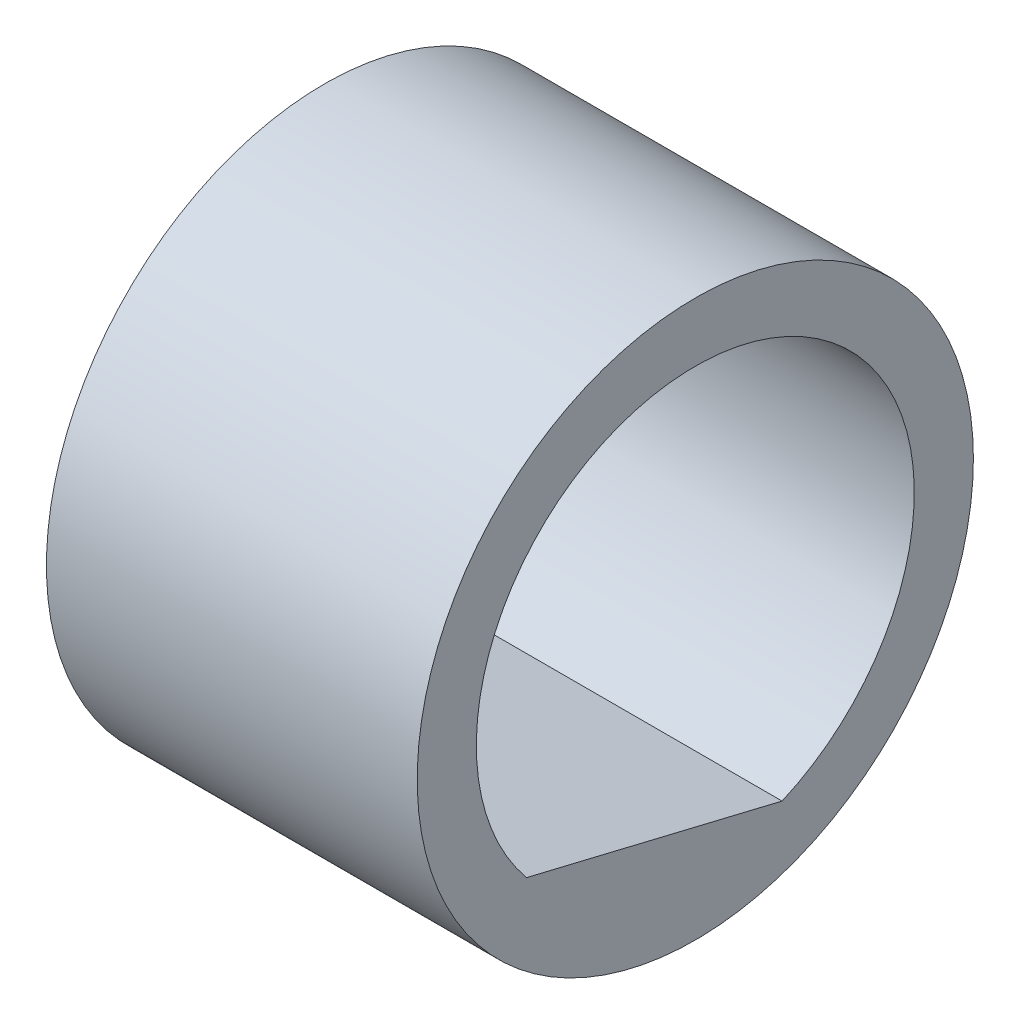
SolidWorks part; units mm, degrees
ref_plane "Front Plane" through (0, 0, 0) normal (0, 0, 1) x (1, 0, 0)
ref_plane "Top Plane" through (0, 0, 0) normal (0, 1, 0) x (1, 0, 0)
ref_plane "Right Plane" through (0, 0, 0) normal (1, 0, 0) x (0, 0, -1)
sketch "Sketch1" plane through (0, 0, 0) normal (1, 0, 0) x (0, 0, -1)
  circle A0 centre (0, 0) radius 3.81
  dimension "D1" = 7.62
extrude "Boss-Extrude1" add sketch "Sketch1" along normal blind 5.08
sketch "Sketch2" plane through (0, 0, 0) normal (-1, 0, 0) x (0, 0, 1)
  line L0 (2.3113, -1.9125) -> (-1.1889, -2.7544) construction
  line L1 (2.3113, -1.9125) -> (-1.1889, -2.7544)
  arc A0 (2.3113, -1.9125) -> (-1.1889, -2.7544) centre (0, 0) ccw construction
  arc A1 (2.3113, -1.9125) -> (-1.1889, -2.7544) centre (0, 0) ccw
extrude "Cut-Extrude1" cut sketch "Sketch2" against normal up to next
equation "\"MDF\"= 0.2in"
equation "\"D1@Boss-Extrude1\"=\"MDF\""
equation "\"TubeR\"= 0.8in"
equation "\"Foamcore\"= 0.2in"
